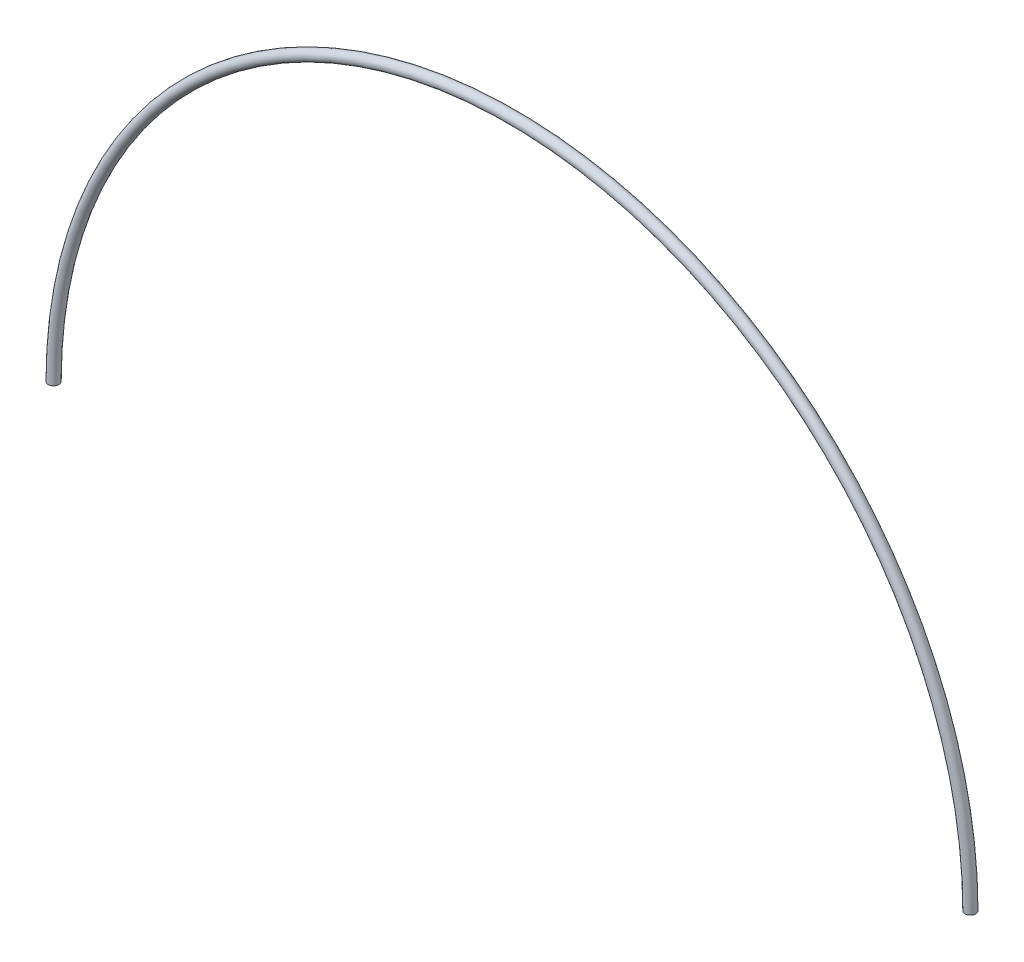
SolidWorks part; units mm, degrees
ref_plane "Front" through (0, 0, 0) normal (0, 0, 1) x (1, 0, 0)
ref_plane "Top" through (0, 0, 0) normal (0, 1, 0) x (1, 0, 0)
ref_plane "Right" through (0, 0, 0) normal (1, 0, 0) x (0, 0, -1)
sketch "Sketch1" plane through (0, 0, 0) normal (0, 0, 1) x (1, 0, 0)
  line L0 (-406.4, 12.7) -> (-406.4, -12.7) construction
  line L1 (419.1, 0) -> (-419.1, 0) construction
  arc A0 (-406.4, 0) -> (406.4, 0) centre (0, 0) cw
ref_plane "Plane1" through (406.4, 0, 0) normal (0, -1, 0) x (1, 0, 0)
sketch "Sketch2" plane through (406.4, 0, 0) normal (0, -1, 0) x (1, 0, 0)
  line L0 (0, -12.7) -> (0, 12.7) construction
  circle A0 centre (0, 0) radius 4.7625
sweep "Sweep1" add profiles "Sketch2" path "Sketch1"
